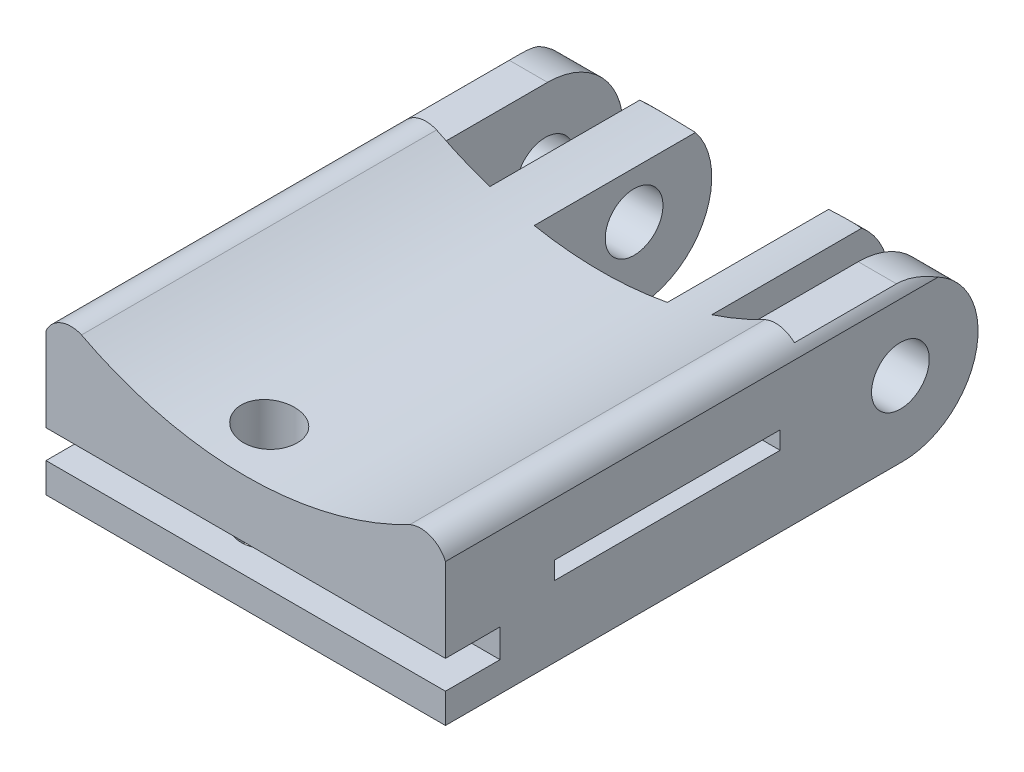
SolidWorks part; units mm, degrees
ref_plane "Front Plane" through (0, 0, 0) normal (0, 0, 1) x (1, 0, 0)
ref_plane "Top Plane" through (0, 0, 0) normal (0, 1, 0) x (1, 0, 0)
ref_plane "Right Plane" through (0, 0, 0) normal (1, 0, 0) x (0, 0, -1)
sketch "Sketch1" plane through (0, 0, 0) normal (0, 1, 0) x (1, 0, 0)
  line L2 (22.5, -50) -> (-22.5, -50)
  line L3 (-17.5, 10) -> (-17.5, -10)
  line L4 (-17.5, -10) -> (-12.5, -10)
  line L5 (-7.5, -10) -> (-2.5, -10)
  line L6 (22.5, 10) -> (22.5, -50)
  line L7 (17.5, -10) -> (12.5, -10)
  line L8 (-22.5, 10) -> (-22.5, -50)
  line L9 (-12.5, 10) -> (-12.5, -10)
  line L10 (-12.5, 10) -> (-7.5, 10)
  line L11 (-7.5, 10) -> (-7.5, -10)
  line L12 (-7.5, -10) -> (-7.5, 10)
  line L13 (2.5, -10) -> (7.5, -10)
  line L15 (-22.5, 10) -> (-17.5, 10)
  line L18 (7.5, -10) -> (2.5, -10)
  line L19 (7.5, 10) -> (7.5, -10)
  line L20 (7.5, 10) -> (12.5, 10)
  line L21 (12.5, 10) -> (12.5, -10)
  line L22 (12.5, -10) -> (12.5, 10)
  line L24 (17.5, 10) -> (17.5, -10)
  line L25 (17.5, -10) -> (17.5, 10)
  line L26 (17.5, 10) -> (22.5, 10)
  line L28 (-12.5, -10) -> (-17.5, -10)
  line L29 (-2.5, -10) -> (-7.5, -10)
  line L30 (12.5, -10) -> (17.5, -10)
  line L36 (-2.5, -10) -> (2.5, -10)
extrude "Boss-Extrude1" add sketch "Sketch1" along normal blind 20
sketch "Sketch2" plane through (0, 0, 50) normal (0, 0, 1) x (1, 0, 0)
  line L0 (-22.5, 20) -> (22.5, 20)
  line L1 (-22.5, 20) -> (-22.5, 16)
  line L2 (-22.5, 20) -> (-22.5, 0) construction
  line L4 (22.5, 20) -> (22.5, 0) construction
  line L5 (22.5, 16) -> (22.5, 20)
  arc A0 (-18.5, 17.6071) -> (18.5, 17.6071) centre (0, 53.0719) ccw
  arc A1 (-22.5, 16) -> (-18.5, 17.6071) centre (-19.6964, 14.8036) cw
  arc A2 (18.5, 17.6071) -> (22.5, 16) centre (19.6964, 14.8036) cw
sketch "Sketch6" plane through (22.5, 0, 0) normal (1, 0, 0) x (0, 0, -1)
  line L0 (1.5, 0) -> (10, 0)
  line L1 (10, 20) -> (10, 0) construction
  line L2 (10, 0) -> (10, 17)
  line L4 (10, 20) -> (-50, 20) construction
  line L5 (61.5, 20) -> (10, 20)
  line L6 (10, 20) -> (10, 0)
  line L14 (1.5, 0) -> (10, 0)
  line L19 (10, 8.5) -> (10, 0)
  line L22 (1.5, 17) -> (-10, 17)
  line L23 (-10, 17) -> (-10, 20)
  line L24 (-10, 20) -> (61.5, 20)
  arc A0 (1.5, 0) -> (1.5, 17) centre (1.5, 8.5) ccw
extrude "Cut-Extrude19" cut sketch "Sketch6" against normal blind 45
extrude "Cut-Extrude23" cut sketch "Sketch2" against normal blind 444
sketch "Sketch10" plane through (-22.5, 0, 0) normal (-1, 0, 0) x (0, 0, 1)
  line L0 (10, 17) -> (10, 0)
  line L1 (-1.5, 0) -> (50, 0) construction
  line L2 (10, 16) -> (-52.0175, 16)
  line L3 (-5.5, 16) -> (50, 16) construction
  line L4 (37.7, 8) -> (12.3, 8)
  line L5 (-303.8357, 10) -> (-303.8357, 8)
  line L6 (-12.3, 8) -> (-37.7, 8)
  line L7 (-354.9085, 8) -> (-329.5085, 8)
  line L8 (-303.8357, 8) -> (-292.2085, 8)
  line L9 (-292.2085, 10) -> (-279.5085, 10)
  line L10 (-12.3, 10) -> (-37.7, 10)
  line L11 (25, 10) -> (12.3, 10)
  line L12 (12.3, 10) -> (12.3, 8)
  line L13 (25, 10) -> (37.7, 10)
  line L14 (-12.3, 10) -> (-12.3, 8)
  line L15 (37.7, 10) -> (37.7, 8)
  line L16 (37.7, 8) -> (12.3, 8)
  line L17 (-37.7, 10) -> (-37.7, 8)
  line L18 (-279.5085, 10) -> (-279.5085, 8)
  line L19 (-242.2085, 10) -> (-254.9085, 10)
  line L20 (-254.9085, 10) -> (-254.9085, 8)
  line L21 (-242.2085, 10) -> (-229.5085, 10)
  line L24 (-279.5085, 10) -> (-292.2085, 10)
  line L25 (-229.5085, 10) -> (-229.5085, 8)
  line L26 (-229.5085, 8) -> (-254.9085, 8)
  line L27 (-329.5085, 10) -> (-342.2085, 10)
  line L28 (-292.2085, 10) -> (-303.8357, 10)
  line L29 (-342.2085, 10) -> (-354.9085, 10)
  line L30 (-354.9085, 10) -> (-354.9085, 8)
  line L31 (-342.2085, 10) -> (-329.5085, 10)
  line L32 (-329.5085, 10) -> (-329.5085, 8)
  line L33 (-329.5085, 8) -> (-354.9085, 8)
  line L34 (-292.2085, 8) -> (-279.5085, 8)
extrude "Cut-Extrude25" cut sketch "Sketch10" against normal blind 45 contours L15 L13 L11 L12 L4 | L10 L17 L6 L14 | L8 L34 L18 L9 L28 L5 | L32 L27 L29 L30 L7 | L26 L20 L19 L21 L25
sketch "Sketch12" plane through (0, 0, 50) normal (0, 0, 1) x (1, 0, 0)
  line L0 (-1, 3.35) -> (-1, 6.55)
  line L3 (1, 3.35) -> (-1, 3.35)
  line L4 (1, 6.55) -> (1, 3.35)
  line L5 (0, 6.55) -> (1, 6.55)
  line L6 (0, 6.55) -> (-1, 6.55)
extrude "Cut-Extrude26" cut sketch "Sketch12" against normal blind 444
sketch "Sketch16" plane through (-22.5, 0, 0) normal (-1, 0, 0) x (0, 0, 1)
  circle A0 centre (-1.25, 8.5) radius 3.25
  circle A2 centre (-386.0585, 2.5888) radius 3.15
extrude "Cut-Extrude28" cut sketch "Sketch16" against normal blind 45
sketch "Sketch18" plane through (0, 0, 0) normal (0, -1, 0) x (1, 0, 0)
  circle A0 centre (-3.5, 43.85) radius 3.15
extrude "Cut-Extrude30" cut sketch "Sketch18" against normal blind 20
sketch "Sketch24" plane through (0, 0, 50) normal (0, 0, 1) x (1, 0, 0)
  line L0 (-1, 6.55) -> (-11, 6.55)
  line L1 (-1, 6.55) -> (1, 6.55)
  line L2 (-1, 3.35) -> (-11, 3.35)
  line L4 (1, 6.55) -> (11, 6.55)
  line L6 (11, 3.35) -> (1, 3.35)
  line L7 (1, 3.35) -> (-1, 3.35)
  line L8 (-11, 6.55) -> (-22.5, 6.55)
  line L9 (-22.5, 16) -> (-22.5, 0) construction
  line L10 (-22.5, 6.55) -> (-22.5, 3.35)
  line L11 (-22.5, 3.35) -> (-11, 3.35)
  line L12 (11, 6.55) -> (22.5, 6.55)
  line L13 (22.5, 16) -> (22.5, 0) construction
  line L14 (22.5, 6.55) -> (22.5, 3.35)
  line L15 (22.5, 3.35) -> (11, 3.35)
extrude "Cut-Extrude31" cut sketch "Sketch24" against normal blind 6.15
